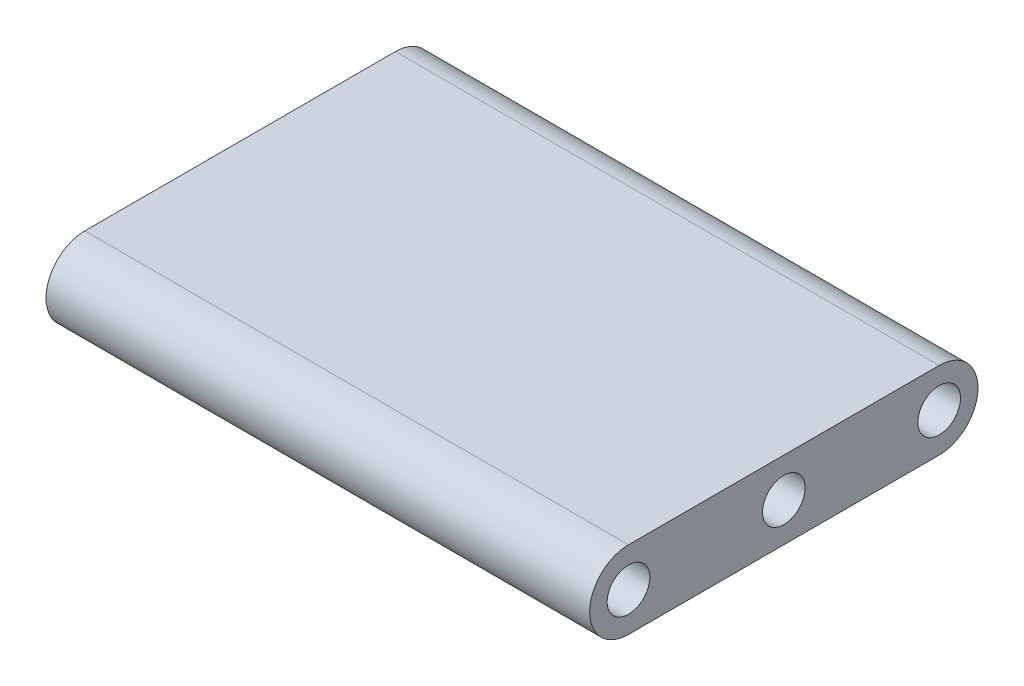
SolidWorks part; units mm, degrees
ref_plane "Front Plane" through (0, 0, 0) normal (0, 0, 1) x (1, 0, 0)
ref_plane "Top Plane" through (0, 0, 0) normal (0, 1, 0) x (1, 0, 0)
ref_plane "Right Plane" through (0, 0, 0) normal (1, 0, 0) x (0, 0, -1)
sketch "Sketch1" plane through (0, 0, 0) normal (1, 0, 0) x (0, 0, -1)
  line L1 (-25.4, -6.35) -> (25.4, -6.35)
  line L2 (-25.4, -6.35) -> (-25.4, 6.35) construction
  line L3 (-25.4, 6.35) -> (25.4, 6.35)
  line L4 (25.4, -6.35) -> (25.4, 6.35) construction
  line L5 (-25.4, -6.35) -> (25.4, 6.35) construction
  line L6 (-25.4, 6.35) -> (25.4, -6.35) construction
  circle A0 centre (-25.4, 0) radius 3.4925
  arc A1 (-25.4, 6.35) -> (-25.4, -6.35) centre (-25.4, 0) ccw
  circle A2 centre (25.4, 0) radius 3.4925
  arc A3 (25.4, -6.35) -> (25.4, 6.35) centre (25.4, 0) ccw
  circle A4 centre (0, 0) radius 3.4925
  point P0 (0, 0)
  dimension "D3" = 6.985
  dimension "D4" = 12.7
  dimension "D1" = 12.7
  dimension "D2" = 50.8
extrude "Boss-Extrude1" add sketch "Sketch1" along normal mid plane 88.9 contours L3 A1 L1 A0 | A2 L3 A0 L1 | L1 A3 L3 A2
